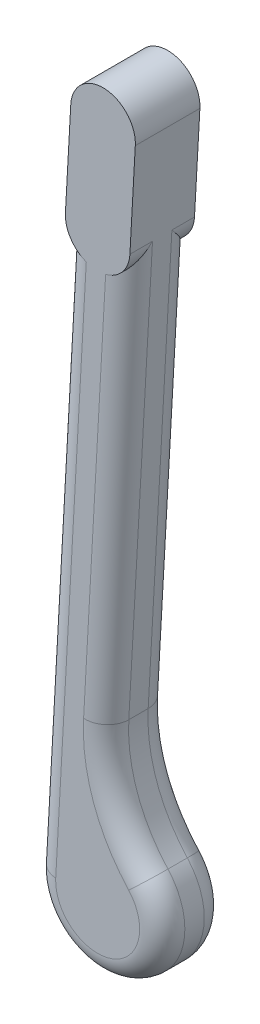
SolidWorks part; units mm, degrees
ref_plane "前视基准面" through (0, 0, 0) normal (0, 0, 1) x (1, 0, 0)
ref_plane "上视基准面" through (0, 0, 0) normal (0, 1, 0) x (1, 0, 0)
ref_plane "右视基准面" through (0, 0, 0) normal (1, 0, 0) x (0, 0, -1)
sketch "草图1" plane through (0, 0, 0) normal (0, 0, 1) x (1, 0, 0)
  line L2 (-9.9846, 0.5556) -> (-19.9691, -178.8889)
  line L3 (9.9846, -0.5556) -> (2.6417, -132.5229)
  arc A1 (2.6417, -132.5229) -> (14.7599, -166.5039) centre (49.0961, -135.1077) ccw
  arc A4 (-19.9691, -178.8889) -> (14.7599, -166.5039) centre (0, -180) ccw
  arc A5 (-9.9846, 0.5556) -> (9.9846, -0.5556) centre (0, 0) cw
extrude "凸台-拉伸1" add sketch "草图1" along normal blind 20
fillet "圆角1" radius 7 10 edges at (-14.9768, -89.1667, 0) (0.5556, 9.9846, 0) (6.3131, -66.5392, 0) (5.2731, -150.7358, 0) (-14.9768, -89.1667, 20) (0.5556, 9.9846, 20) (6.3131, -66.5392, 20) (5.2731, -150.7358, 20) (6.718, -198.838, 0) (6.718, -198.838, 20)
sketch "草图2" plane through (0, 0, 0) normal (0, 0, 1) x (1, 0, 0)
  line L1 (-9.9846, 0.5556) -> (-8.3179, 30.5092)
  line L4 (11.6512, 29.3981) -> (9.9846, -0.5556)
  arc A2 (-8.3179, 30.5092) -> (11.6512, 29.3981) centre (1.6667, 29.9537) cw
  arc A3 (-9.9846, 0.5556) -> (9.9846, -0.5556) centre (0, 0) ccw
extrude "凸台-拉伸2" add sketch "草图2" along normal blind 20
sketch3d "3D草图1"
  line L0 (-9.9846, 0.5556, 20) -> (9.9846, -0.5556, 20) construction
  line L1 (9.9846, -0.5556, 0) -> (-9.9846, 0.5556, 0) construction
  line L2 (0, 0, 0) -> (0, 0, 20) construction
ref_point "点1"
